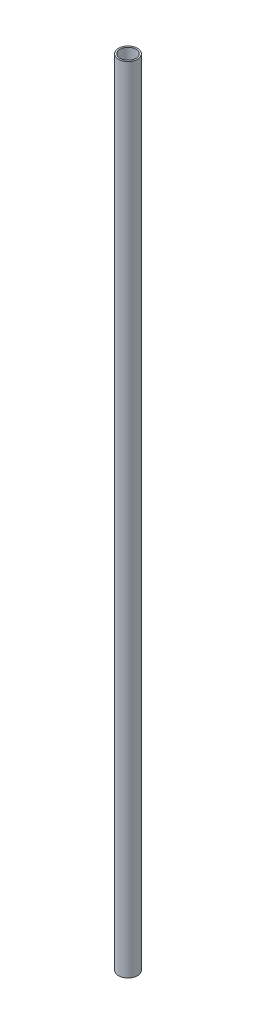
SolidWorks part; units mm, degrees
ref_plane "Front Plane" through (0, 0, 0) normal (0, 0, 1) x (1, 0, 0)
ref_plane "Top Plane" through (0, 0, 0) normal (0, 1, 0) x (1, 0, 0)
ref_plane "Right Plane" through (0, 0, 0) normal (1, 0, 0) x (0, 0, -1)
sketch "Sketch1" plane through (0, 0, 0) normal (0, 1, 0) x (1, 0, 0)
  circle A0 centre (0, 0) radius 6
  circle A1 centre (0, 0) radius 5
  dimension "D1" = 12
  dimension "D2" = 10
extrude "Boss-Extrude1" add sketch "Sketch1" along normal blind 500
